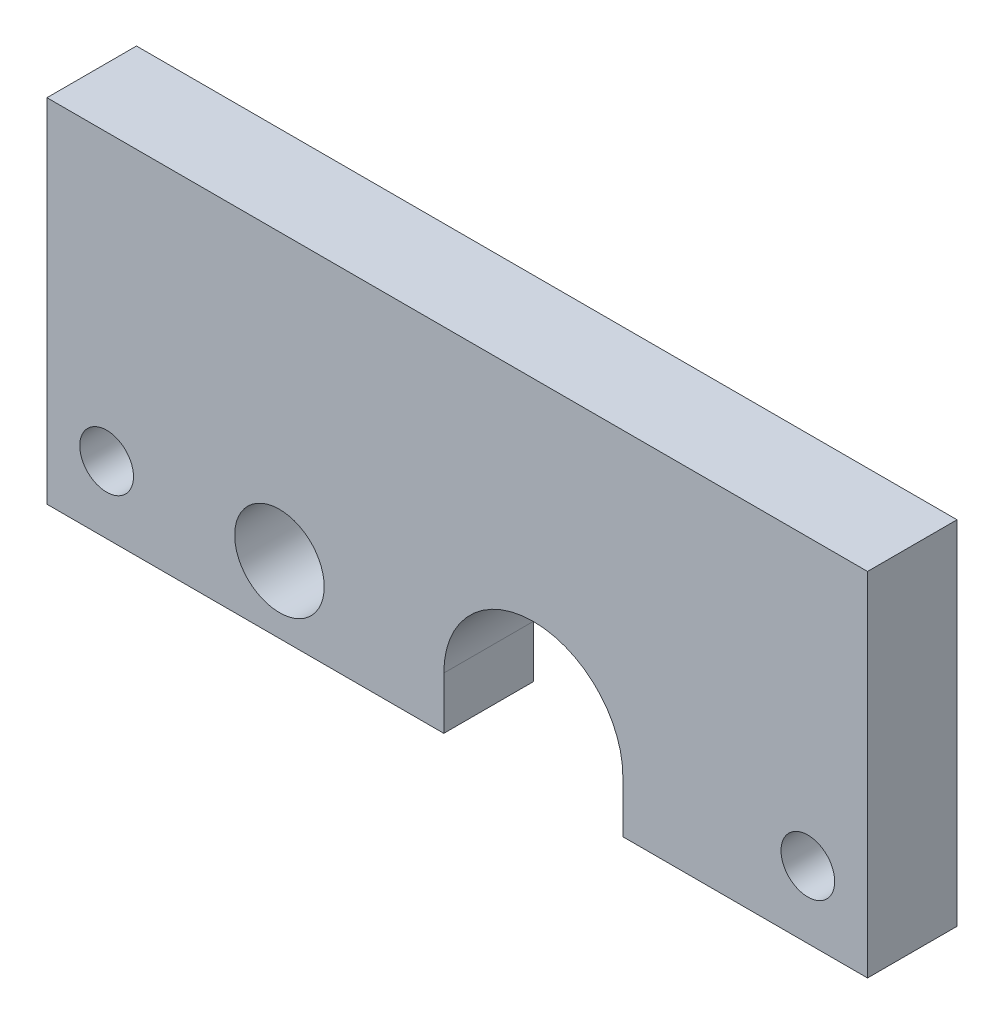
SolidWorks part; units mm, degrees
ref_plane "Plano frontal" through (0, 0, 0) normal (0, 0, 1) x (1, 0, 0)
ref_plane "Plano superior" through (0, 0, 0) normal (0, 1, 0) x (1, 0, 0)
ref_plane "Plano direito" through (0, 0, 0) normal (1, 0, 0) x (0, 0, -1)
sketch "Model" plane through (0, 0, 0) normal (0, 0, 1) x (1, 0, 0)
  line L0 (27.2842, 8.3068) -> (27.2842, 31.9068)
  line L1 (27.2842, 8.3068) -> (53.8842, 8.3068)
  line L2 (53.8842, 11.8068) -> (53.8842, 8.3068)
  line L3 (65.8842, 11.8068) -> (65.8842, 8.3068)
  line L4 (65.8842, 8.3068) -> (82.2842, 8.3068)
  line L5 (82.2842, 31.9068) -> (82.2842, 8.3068)
  line L6 (27.2842, 31.9068) -> (82.2842, 31.9068)
  circle A0 centre (78.2842, 12.8068) radius 1.8
  circle A1 centre (42.8656, 12.8068) radius 3
  circle A2 centre (31.2842, 12.8068) radius 1.8
  arc A3 (65.8842, 11.8068) -> (53.8842, 11.8068) centre (59.8842, 11.8068) ccw
extrude "Ressalto-extrusão1" add sketch "Model" along normal blind 6
